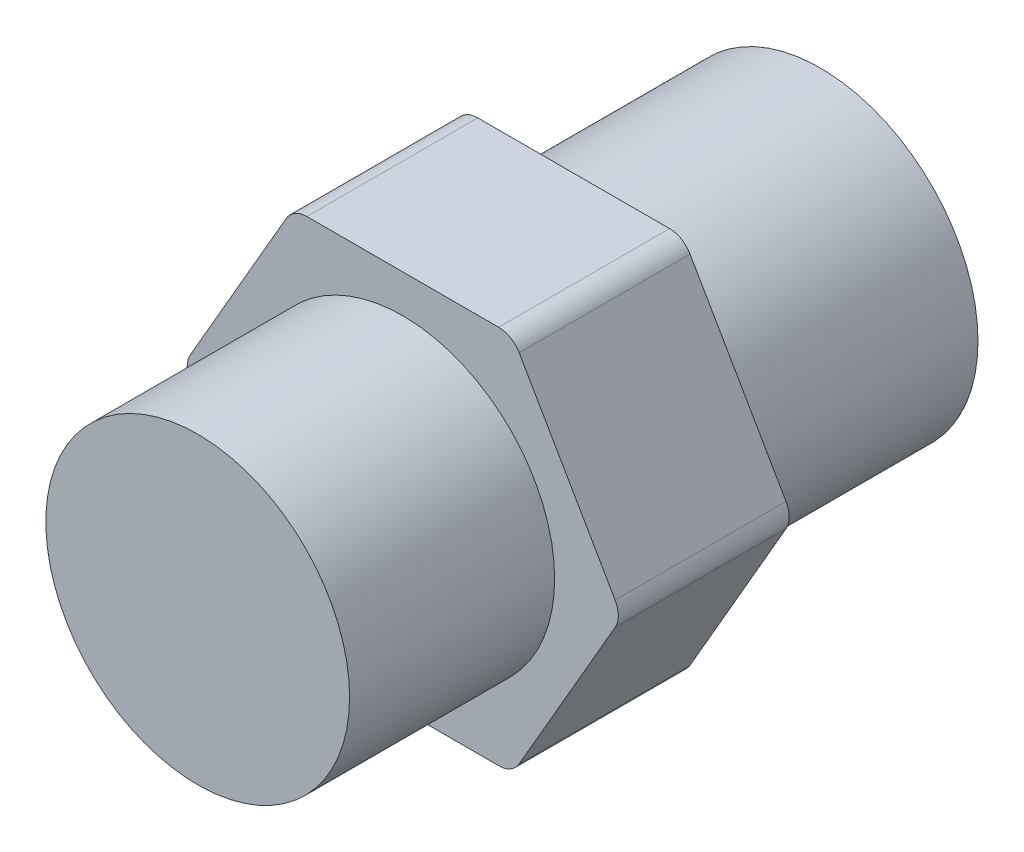
SolidWorks part; units mm, degrees
material "Brass"
ref_plane "Front Plane" through (0, 0, 0) normal (0, 0, 1) x (1, 0, 0)
ref_plane "Top Plane" through (0, 0, 0) normal (0, 1, 0) x (1, 0, 0)
ref_plane "Right Plane" through (0, 0, 0) normal (1, 0, 0) x (0, 0, -1)
sketch "Sketch1" plane through (0, 0, 0) normal (0, 0, 1) x (1, 0, 0)
  line L8 (14.6647, 0) -> (7.3323, 12.7)
  line L9 (7.3323, 12.7) -> (-7.3323, 12.7)
  line L10 (-7.3323, 12.7) -> (-14.6647, 0)
  line L11 (-14.6647, 0) -> (-7.3323, -12.7)
  line L12 (-7.3323, -12.7) -> (7.3323, -12.7)
  line L13 (7.3323, -12.7) -> (14.6647, 0)
  circle A0 centre (0, 0) radius 12.7 construction
  dimension "D1" = 25.4
extrude "Boss-Extrude1" add sketch "Sketch1" along normal blind 11.43
sketch "Sketch4" plane through (-10.9985, -6.35, 0) normal (-0.866, -0.5, 0) x (0, 0, 1)
  line L0 (5.715, 7.3323) -> (5.715, -7.3323)
  line L1 (11.43, 7.3323) -> (0, 7.3323) construction
  line L2 (11.43, -7.3323) -> (0, -7.3323) construction
  line L3 (0, 0) -> (11.43, 0)
  line L4 (0, 7.3323) -> (0, -7.3323) construction
  line L5 (11.43, 7.3323) -> (11.43, -7.3323) construction
  line L7 (5.715, 5.5726) -> (0.889, 2.7863)
  line L8 (0.889, 2.7863) -> (0.889, -2.7863)
  line L9 (0.889, -2.7863) -> (5.715, -5.5726)
  line L10 (5.715, -5.5726) -> (10.541, -2.7863)
  line L11 (10.541, -2.7863) -> (10.541, 2.7863)
  line L12 (10.541, 2.7863) -> (5.715, 5.5726)
  circle A0 centre (5.715, 0) radius 4.826 construction
extrude "Boss-Extrude2" add sketch "Sketch4" along normal blind 6.35 contours L7 L8 L3 L0 | L8 L9 L0 L3 | L10 L11 L3 L0 | L11 L12 L0 L3
sketch "Sketch6" plane through (0, 0, 11.43) normal (0, 0, 1) x (1, 0, 0)
  circle A0 centre (0, 0) radius 10.16
extrude "Boss-Extrude3" add sketch "Sketch6" along normal blind 13.716
sketch "Sketch7" plane through (0, 0, 0) normal (0, 0, -1) x (-1, 0, 0)
  circle A0 centre (0, 0) radius 10.541
extrude "Boss-Extrude4" add sketch "Sketch7" along normal blind 16.51
fillet "Fillet1" radius 1.5875 6 edges at (-14.6647, 0, 5.715) (-7.3323, 12.7, 5.715) (7.3323, 12.7, 5.715) (14.6647, 0, 5.715) (-7.3323, -12.7, 5.715) (7.3323, -12.7, 5.715)
fillet "Fillet2" radius 1.5875 6 edges at (-15.1413, -5.5245, 0.889) (-12.355, -10.3505, 0.889) (-10.9619, -12.7635, 5.715) (-12.355, -10.3505, 10.541) (-15.1413, -5.5245, 10.541) (-16.5344, -3.1115, 5.715)
ref_plane "Plane1" through (3.2079, -5.5563, 0) normal (-0.5, 0.866, 0) x (-0.866, -0.5, 0)
